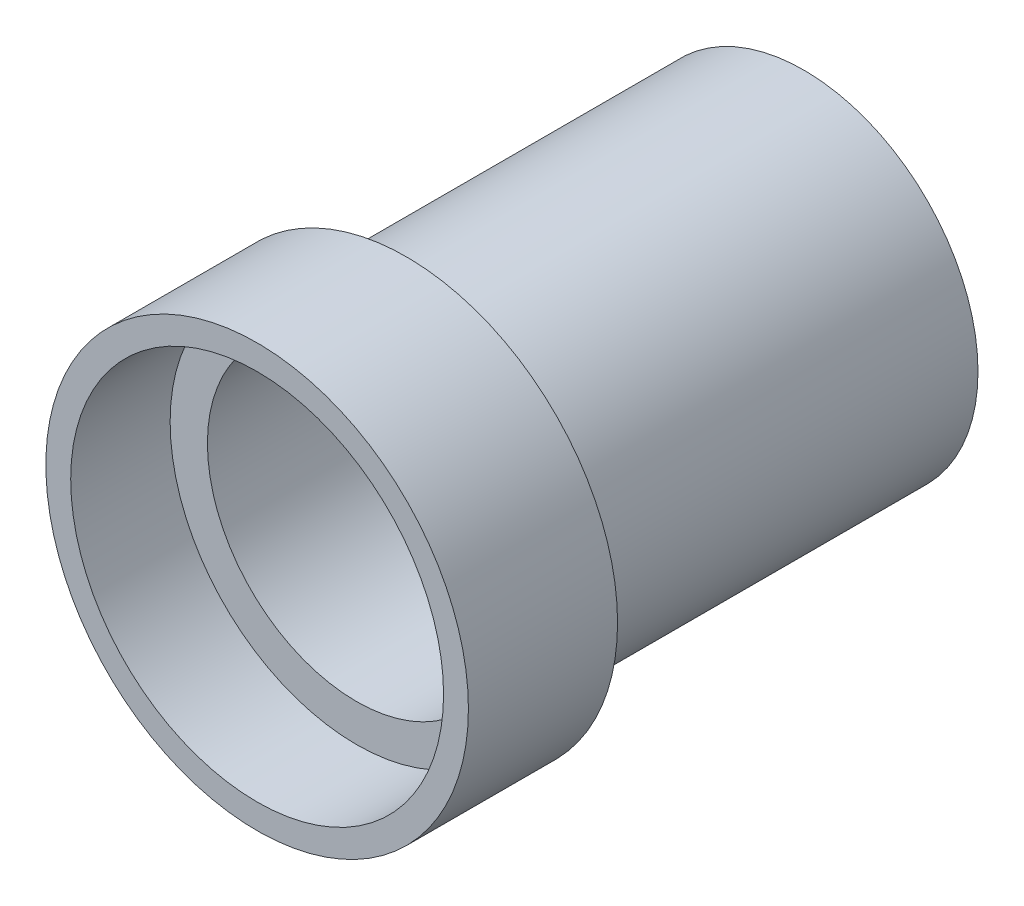
SolidWorks part; units mm, degrees
ref_plane "前视基准面" through (0, 0, 0) normal (0, 0, 1) x (1, 0, 0)
ref_plane "上视基准面" through (0, 0, 0) normal (0, 1, 0) x (1, 0, 0)
ref_plane "右视基准面" through (0, 0, 0) normal (1, 0, 0) x (0, 0, -1)
sketch "草图1" plane through (0, 0, 0) normal (0, 0, 1) x (1, 0, 0)
  circle A0 centre (0, 0) radius 7
  dimension "D1" = 14
extrude "凸台-拉伸1" add sketch "草图1" along normal blind 16
sketch "草图2" plane through (0, 0, 16) normal (0, 0, 1) x (1, 0, 0)
  circle A0 centre (0, 0) radius 8.5
  dimension "D1" = 17
extrude "凸台-拉伸2" add sketch "草图2" along normal blind 6
sketch "草图3" plane through (0, 0, 22) normal (0, 0, 1) x (1, 0, 0)
  circle A0 centre (0, 0) radius 7.5
  dimension "D1" = 15
extrude "切除-拉伸1" cut sketch "草图3" against normal blind 4
sketch "草图4" plane through (0, 0, 0) normal (0, 0, -1) x (-1, 0, 0)
  circle A0 centre (0, 0) radius 6
  dimension "D1" = 12
extrude "切除-拉伸2" cut sketch "草图4" against normal blind 25
